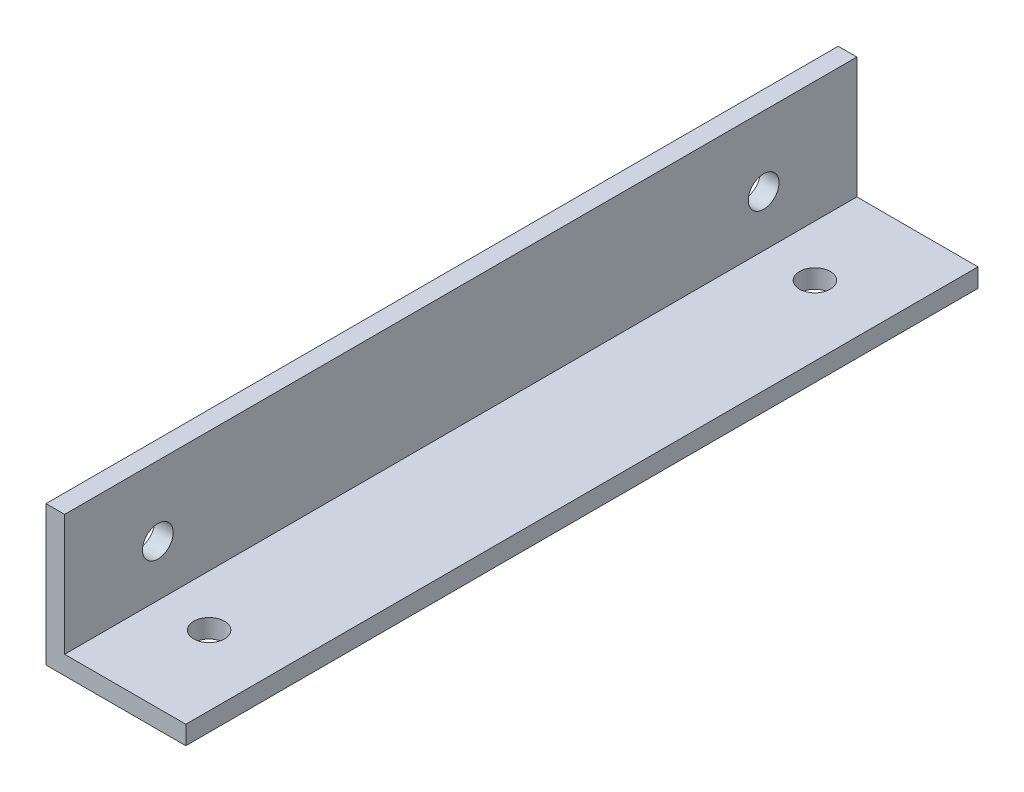
SolidWorks part; units mm, degrees
ref_plane "正面" through (0, 0, 0) normal (0, 0, 1) x (1, 0, 0)
ref_plane "平面" through (0, 0, 0) normal (0, 1, 0) x (1, 0, 0)
ref_plane "右側面" through (0, 0, 0) normal (1, 0, 0) x (0, 0, -1)
sketch "ｽｹｯﾁ1" plane through (0, 0, 0) normal (0, 0, 1) x (1, 0, 0)
  line L0 (0, 0) -> (0, 15)
  line L1 (0, 15) -> (2, 15)
  line L2 (2, 15) -> (2, 2)
  line L3 (2, 2) -> (15, 2)
  line L4 (15, 2) -> (15, 0)
  line L5 (15, 0) -> (0, 0)
  dimension "D1" = 15
  dimension "D2" = 15
  dimension "D3" = 13
  dimension "D4" = 2
  dimension "D5" = 2
extrude "ﾎﾞｽ - 押し出し1" add sketch "ｽｹｯﾁ1" along normal blind 85
sketch "ｽｹｯﾁ2" plane through (0, 0, 0) normal (0, -1, 0) x (1, 0, 0)
  line L0 (7.5, 0) -> (7.5, 10)
  line L1 (0, 0) -> (15, 0) construction
  line L2 (7.5, 10) -> (7.5, 75)
  circle A0 centre (7.5, 10) radius 2.2
  circle A1 centre (7.5, 75) radius 2.2
  dimension "D3" = 4.4
  dimension "D4" = 4.4
  dimension "D1" = 10
  dimension "D2" = 65
sketch "ｽｹｯﾁ3" plane through (0, 0, 0) normal (-1, 0, 0) x (0, 0, 1)
  line L0 (0, 7.5) -> (10, 7.5)
  line L1 (0, 15) -> (0, 0) construction
  line L2 (10, 7.5) -> (75, 7.5)
  circle A0 centre (10, 7.5) radius 2.2
  circle A1 centre (75, 7.5) radius 2.2
  dimension "D3" = 4.4
  dimension "D4" = 4.4
  dimension "D1" = 10
  dimension "D2" = 65
hole_wizard "M4x0.7 ねじ穴1" positions "3Dｽｹｯﾁ1" profile "ｽｹｯﾁ4" tap size "M4x0.7" standard "JIS"
sketch3d "3Dｽｹｯﾁ1"
  point P0 (0, 7.5, 75)
  point P3 (7.5, 0, 75)
  point P6 (7.5, 0, 10)
  point P9 (0, 7.5, 10)
sketch "ｽｹｯﾁ4" plane through (0, 7.5, 75) normal (0, 1, 0) x (0, 0, 1)
  line L0 (0, 0) -> (0, 12.4914)
  line L1 (0, 12.4914) -> (1.65, 11.5)
  line L2 (1.65, 11.5) -> (1.65, 0)
  line L5 (1.65, 0) -> (0, 0)
  line L10 (0, 12.4914) -> (-1.65, 11.5) construction
  line L11 (0, -6.35) -> (0, 107.95) construction
  dimension "ねじ下穴ﾄﾞﾘﾙ直径" = 3.3
  dimension "ねじ下穴ﾄﾞﾘﾙの深さ" = 11.5
  dimension "ﾄﾞﾘﾙ角度" = 118
cosmetic thread "穴のねじ山1" parameters "D1"=2, "D2"=4
cosmetic thread "穴のねじ山2" parameters "D1"=2, "D2"=4
cosmetic thread "穴のねじ山3" parameters "D1"=2, "D2"=4
cosmetic thread "穴のねじ山4" parameters "D1"=2, "D2"=4
